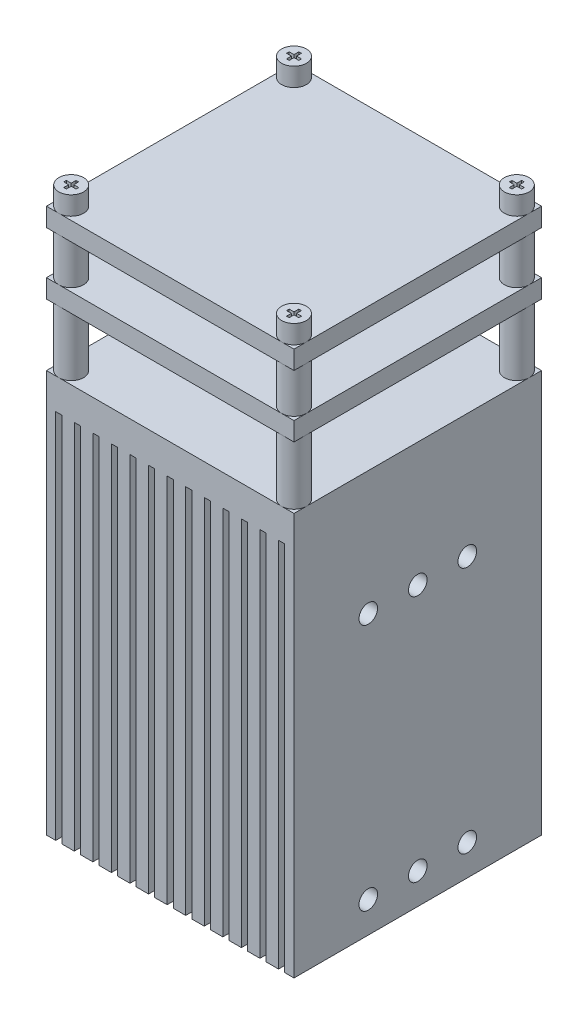
SolidWorks part; units mm, degrees
ref_plane "Front" through (0, 0, 0) normal (0, 0, 1) x (1, 0, 0)
ref_plane "Top" through (0, 0, 0) normal (0, 1, 0) x (1, 0, 0)
ref_plane "Right" through (0, 0, 0) normal (1, 0, 0) x (0, 0, -1)
sketch "Sketch1" plane through (0, 0, 0) normal (0, 1, 0) x (1, 0, 0)
  line L1 (-20, 20) -> (20, 20)
  line L2 (-20, 20) -> (-20, -20)
  line L3 (-20, -20) -> (20, -20)
  line L4 (20, 20) -> (20, -20)
  line L5 (-20, 20) -> (20, -20) construction
  line L6 (-20, -20) -> (20, 20) construction
  point P0 (0, 0)
  dimension "D1" = 40
  dimension "D2" = 40
extrude "Boss-Extrude1" add sketch "Sketch1" along normal blind 65
sketch "Sketch2" plane through (0, 0, 0) normal (0, -1, 0) x (-1, 0, 0)
  circle A0 centre (0, 0) radius 7
  circle A1 centre (0, 0) radius 2
extrude "Boss-Extrude2" add sketch "Sketch2" along normal blind 10
sketch "Sketch3" plane through (20, 0, 0) normal (1, 0, 0) x (0, 0, -1)
  line L0 (0, 79.0948) -> (0, 14.3901) construction
  line L1 (-43.0564, 25) -> (45.3015, 25) construction
  line L3 (-20, 0) -> (20, 0) construction
  circle A0 centre (0, 45) radius 1.5
  circle A1 centre (-8, 45) radius 1.5
  circle A2 centre (8, 45) radius 1.5
  circle A3 centre (8, 5) radius 1.5
  circle A4 centre (0, 5) radius 1.5
  circle A5 centre (-8, 5) radius 1.5
  dimension "D1" = 8
  dimension "D2" = 20
  dimension "D3" = 25
extrude "Cut-Extrude1" cut sketch "Sketch3" against normal blind 10
sketch "Sketch4" plane through (0, 65, 0) normal (0, 1, 0) x (1, 0, 0)
  line L0 (-20, -20) -> (20, -20) construction
  line L1 (20, -20) -> (20, 20) construction
  circle A0 centre (18, -18) radius 2
  circle A1 centre (-18, -18) radius 2
  circle A2 centre (-18, 18) radius 2
  circle A3 centre (18, 18) radius 2
  dimension "D1" = 4
  dimension "D2" = 4
extrude "Boss-Extrude3" add sketch "Sketch4" along normal blind 10
sketch "Sketch5" plane through (0, 75, 0) normal (0, 1, 0) x (1, 0, 0)
  line L1 (-20, 20) -> (20, 20)
  line L2 (-20, 20) -> (-20, -20)
  line L3 (-20, -20) -> (20, -20)
  line L4 (20, 20) -> (20, -20)
  line L5 (-20, 20) -> (20, -20) construction
  line L6 (-20, -20) -> (20, 20) construction
  point P0 (0, 0)
extrude "Boss-Extrude4" add sketch "Sketch5" along normal blind 3
pattern_linear "LPattern1" count 2 spacing 10 along (0, 1, 0) of "Boss-Extrude3", "Boss-Extrude4"
sketch "Sketch6" plane through (0, 88, 0) normal (0, 1, 0) x (1, 0, 0)
  line L1 (20, -20) -> (20, 20) construction
  line L2 (-20, -20) -> (20, -20) construction
  line L3 (-17.7875, -18.9966) -> (-17.7875, -18.2125)
  line L4 (17.7875, -17.0034) -> (18.2125, -17.0034)
  line L5 (17.7875, -17.0034) -> (17.7875, -17.7875)
  line L6 (17.7875, -18.9966) -> (18.2125, -18.9966)
  line L7 (18.2125, -17.0034) -> (18.2125, -17.7875)
  line L8 (-17.0034, -18.2125) -> (-17.7875, -18.2125)
  line L9 (-17.0034, -17.7875) -> (-17.0034, -18.2125)
  line L10 (-17.0034, -17.7875) -> (-17.7875, -17.7875)
  line L11 (18.9966, -17.7875) -> (18.2125, -17.7875)
  line L12 (18.9966, -17.7875) -> (18.9966, -18.2125)
  line L13 (18.9966, -18.2125) -> (18.2125, -18.2125)
  line L14 (17.0034, -17.7875) -> (17.0034, -18.2125)
  line L15 (17.7875, -17.7875) -> (17.0034, -17.7875)
  line L21 (17.7875, -18.2125) -> (17.7875, -18.9966)
  line L23 (18.2125, -18.2125) -> (18.2125, -18.9966)
  line L24 (17.7875, -18.2125) -> (17.0034, -18.2125)
  line L25 (-17.7875, -17.7875) -> (-17.7875, -17.0034)
  line L26 (-17.7875, -17.0034) -> (-18.2125, -17.0034)
  line L27 (-18.2125, -17.7875) -> (-18.2125, -17.0034)
  line L28 (-18.2125, -17.7875) -> (-18.9966, -17.7875)
  line L29 (-18.9966, -17.7875) -> (-18.9966, -18.2125)
  line L30 (-18.2125, -18.2125) -> (-18.9966, -18.2125)
  line L31 (-18.2125, -18.9966) -> (-18.2125, -18.2125)
  line L32 (-17.7875, -18.9966) -> (-18.2125, -18.9966)
  line L33 (-18.9966, 17.7875) -> (-18.2125, 17.7875)
  line L34 (-18.2125, 17.0034) -> (-18.2125, 17.7875)
  line L35 (-17.7875, 17.0034) -> (-18.2125, 17.0034)
  line L36 (-17.7875, 17.0034) -> (-17.7875, 17.7875)
  line L37 (-17.7875, 17.7875) -> (-17.0034, 17.7875)
  line L38 (-17.0034, 17.7875) -> (-17.0034, 18.2125)
  line L39 (-17.7875, 18.2125) -> (-17.0034, 18.2125)
  line L40 (-17.7875, 18.2125) -> (-17.7875, 18.9966)
  line L41 (-17.7875, 18.9966) -> (-18.2125, 18.9966)
  line L42 (-18.2125, 18.2125) -> (-18.2125, 18.9966)
  line L43 (-18.9966, 18.2125) -> (-18.2125, 18.2125)
  line L44 (-18.9966, 17.7875) -> (-18.9966, 18.2125)
  line L45 (17.7875, 18.9966) -> (17.7875, 18.2125)
  line L46 (17.0034, 18.2125) -> (17.7875, 18.2125)
  line L47 (17.0034, 17.7875) -> (17.0034, 18.2125)
  line L48 (17.0034, 17.7875) -> (17.7875, 17.7875)
  line L49 (17.7875, 17.7875) -> (17.7875, 17.0034)
  line L50 (17.7875, 17.0034) -> (18.2125, 17.0034)
  line L51 (18.2125, 17.7875) -> (18.2125, 17.0034)
  line L52 (18.2125, 17.7875) -> (18.9966, 17.7875)
  line L53 (18.9966, 17.7875) -> (18.9966, 18.2125)
  line L54 (18.2125, 18.2125) -> (18.9966, 18.2125)
  line L55 (18.2125, 18.9966) -> (18.2125, 18.2125)
  line L56 (17.7875, 18.9966) -> (18.2125, 18.9966)
  circle A0 centre (18, -18) radius 2
  circle A1 centre (-18, -18) radius 2
  circle A2 centre (-18, 18) radius 2
  circle A3 centre (18, 18) radius 2
  dimension "D1" = 2
  dimension "D2" = 4
extrude "Boss-Extrude5" add sketch "Sketch6" along normal blind 3
sketch "Sketch7" plane through (-20, 0, 0) normal (-1, 0, 0) x (0, 0, 1)
  line L0 (-7, 0) -> (7, 0) construction
  line L1 (-0.5, 60) -> (0.5, 60)
  line L2 (-0.5, 60) -> (-0.5, 0)
  line L3 (-0.5, 0) -> (0.5, 0)
  line L4 (0.5, 60) -> (0.5, 0)
  line L5 (-0.5, 60) -> (0.5, 0) construction
  line L6 (-0.5, 0) -> (0.5, 60) construction
  line L7 (2.5, 60) -> (3.5, 0) construction
  line L8 (2.5, 60) -> (2.5, 0)
  line L9 (2.5, 60) -> (3.5, 60)
  line L10 (3.5, 60) -> (3.5, 0)
  line L11 (2.5, 0) -> (3.5, 0)
  line L12 (5.5, 60) -> (6.5, 0) construction
  line L13 (5.5, 60) -> (5.5, 0)
  line L14 (5.5, 60) -> (6.5, 60)
  line L15 (6.5, 60) -> (6.5, 0)
  line L16 (5.5, 0) -> (6.5, 0)
  line L17 (8.5, 60) -> (9.5, 0) construction
  line L18 (8.5, 60) -> (8.5, 0)
  line L19 (8.5, 60) -> (9.5, 60)
  line L20 (9.5, 60) -> (9.5, 0)
  line L21 (8.5, 0) -> (9.5, 0)
  line L22 (11.5, 60) -> (12.5, 0) construction
  line L23 (11.5, 60) -> (11.5, 0)
  line L24 (11.5, 60) -> (12.5, 60)
  line L25 (12.5, 60) -> (12.5, 0)
  line L26 (11.5, 0) -> (12.5, 0)
  line L27 (14.5, 60) -> (15.5, 0) construction
  line L28 (14.5, 60) -> (14.5, 0)
  line L29 (14.5, 60) -> (15.5, 60)
  line L30 (15.5, 60) -> (15.5, 0)
  line L31 (14.5, 0) -> (15.5, 0)
  line L32 (17.5, 60) -> (18.5, 0) construction
  line L33 (17.5, 60) -> (17.5, 0)
  line L34 (17.5, 60) -> (18.5, 60)
  line L35 (18.5, 60) -> (18.5, 0)
  line L36 (17.5, 0) -> (18.5, 0)
  line L37 (1.4994, 0.0333) -> (0.5, 0)
  line L38 (-1.4994, 59.9667) -> (0.5, 0)
  line L39 (-0.5, 60) -> (-1.4994, 59.9667)
  line L40 (-0.5, 60) -> (1.4994, 0.0333)
  line L41 (-3.5, 60) -> (-3.5, 0)
  line L42 (-3.5, 60) -> (-2.5, 60)
  line L43 (-2.5, 60) -> (-2.5, 0)
  line L44 (-3.5, 0) -> (-2.5, 0)
  line L45 (-6.5, 60) -> (-6.5, 0)
  line L46 (-6.5, 60) -> (-5.5, 60)
  line L47 (-5.5, 60) -> (-5.5, 0)
  line L48 (-6.5, 0) -> (-5.5, 0)
  line L49 (-9.5, 60) -> (-9.5, 0)
  line L50 (-9.5, 60) -> (-8.5, 60)
  line L51 (-8.5, 60) -> (-8.5, 0)
  line L52 (-9.5, 0) -> (-8.5, 0)
  line L53 (-12.5, 60) -> (-12.5, 0)
  line L54 (-12.5, 60) -> (-11.5, 60)
  line L55 (-11.5, 60) -> (-11.5, 0)
  line L56 (-12.5, 0) -> (-11.5, 0)
  line L57 (-15.5, 60) -> (-15.5, 0)
  line L58 (-15.5, 60) -> (-14.5, 60)
  line L59 (-14.5, 60) -> (-14.5, 0)
  line L60 (-15.5, 0) -> (-14.5, 0)
  line L61 (-18.5, 60) -> (-18.5, 0)
  line L62 (-18.5, 60) -> (-17.5, 60)
  line L63 (-17.5, 60) -> (-17.5, 0)
  line L64 (-18.5, 0) -> (-17.5, 0)
  point P0 (0, 30)
  line M5 (-20, 0) -> (20, 0)
  line M7 (20, 65) -> (18, 65)
  line M8 (18, 65) -> (-18, 65)
  line M9 (-18, 65) -> (-20, 65)
  dimension "D1" = 1
  dimension "D2" = 7
  dimension "D3" = 7
extrude "Cut-Extrude2" cut sketch "Sketch7" against normal blind 1 contours L59 L57 M8 M5 | L55 L53 M8 M5 | L51 L49 M8 M5 | L47 L45 M8 M5 | L43 L41 M8 M5 | L38 L2 M5 | L10 L8 M8 M5 | L15 L13 M8 M5 | L20 L18 M8 M5 | L25 L23 M8 M5 | L30 L28 M8 M5 | L35 L33 M7 M8 M5 | L40 L2 L38 L4 | L63 L61 M8 M9 M5
sketch "Sketch8" plane through (0, 0, -20) normal (0, 0, -1) x (-1, 0, 0)
  line L0 (-7, 0) -> (7, 0) construction
  line L1 (-0.5, 60) -> (0.5, 60)
  line L2 (-0.5, 60) -> (-0.5, 0)
  line L3 (-0.5, 0) -> (0.5, 0)
  line L4 (0.5, 60) -> (0.5, 0)
  line L5 (-0.5, 60) -> (0.5, 0) construction
  line L6 (-0.5, 0) -> (0.5, 60) construction
  line L7 (2.5, 60) -> (2.5, 0)
  line L8 (2.5, 60) -> (3.5, 60)
  line L9 (3.5, 60) -> (3.5, 0)
  line L10 (2.5, 0) -> (3.5, 0)
  line L11 (5.5, 60) -> (5.5, 0)
  line L12 (5.5, 60) -> (6.5, 60)
  line L13 (6.5, 60) -> (6.5, 0)
  line L14 (5.5, 0) -> (6.5, 0)
  line L15 (8.5, 60) -> (8.5, 0)
  line L16 (8.5, 60) -> (9.5, 60)
  line L17 (9.5, 60) -> (9.5, 0)
  line L18 (8.5, 0) -> (9.5, 0)
  line L19 (11.5, 60) -> (11.5, 0)
  line L20 (11.5, 60) -> (12.5, 60)
  line L21 (12.5, 60) -> (12.5, 0)
  line L22 (11.5, 0) -> (12.5, 0)
  line L23 (14.5, 60) -> (14.5, 0)
  line L24 (14.5, 60) -> (15.5, 60)
  line L25 (15.5, 60) -> (15.5, 0)
  line L26 (14.5, 0) -> (15.5, 0)
  line L27 (17.5, 60) -> (17.5, 0)
  line L28 (17.5, 60) -> (18.5, 60)
  line L29 (18.5, 60) -> (18.5, 0)
  line L30 (17.5, 0) -> (18.5, 0)
  line L31 (-3.5, 60) -> (-3.5, 0)
  line L32 (-3.5, 60) -> (-2.5, 60)
  line L33 (-2.5, 60) -> (-2.5, 0)
  line L34 (-3.5, 0) -> (-2.5, 0)
  line L35 (-6.5, 60) -> (-6.5, 0)
  line L36 (-6.5, 60) -> (-5.5, 60)
  line L37 (-5.5, 60) -> (-5.5, 0)
  line L38 (-6.5, 0) -> (-5.5, 0)
  line L39 (-9.5, 60) -> (-9.5, 0)
  line L40 (-9.5, 60) -> (-8.5, 60)
  line L41 (-8.5, 60) -> (-8.5, 0)
  line L42 (-9.5, 0) -> (-8.5, 0)
  line L43 (-12.5, 60) -> (-12.5, 0)
  line L44 (-12.5, 60) -> (-11.5, 60)
  line L45 (-11.5, 60) -> (-11.5, 0)
  line L46 (-12.5, 0) -> (-11.5, 0)
  line L47 (-15.5, 60) -> (-15.5, 0)
  line L48 (-15.5, 60) -> (-14.5, 60)
  line L49 (-14.5, 60) -> (-14.5, 0)
  line L50 (-15.5, 0) -> (-14.5, 0)
  line L51 (-18.5, 60) -> (-18.5, 0)
  line L52 (-18.5, 60) -> (-17.5, 60)
  line L53 (-17.5, 60) -> (-17.5, 0)
  line L54 (-18.5, 0) -> (-17.5, 0)
  point P0 (0, 30)
  line M5 (-20, 0) -> (20, 0)
  line M7 (20, 65) -> (18, 65)
  line M8 (18, 65) -> (-18, 65)
  dimension "D1" = 1
  dimension "D2" = 7
  dimension "D3" = 7
extrude "Cut-Extrude3" cut sketch "Sketch8" against normal blind 1 contours L49 L47 M8 M5 | L45 L43 M8 M5 | L41 L39 M8 M5 | L37 L35 M8 M5 | L33 L31 M8 M5 | L4 L2 M8 M5 | L9 L7 M8 M5 | L13 L11 M8 M5 | L17 L15 M8 M5 | L21 L19 M8 M5 | L29 L27 M7 M8 M5 | L51 L54 L53 L52 | L23 L26 L25 L24
mirror "Mirror1" about plane through (0, 0, 0) normal (0, 0, 1) of "Cut-Extrude3"
